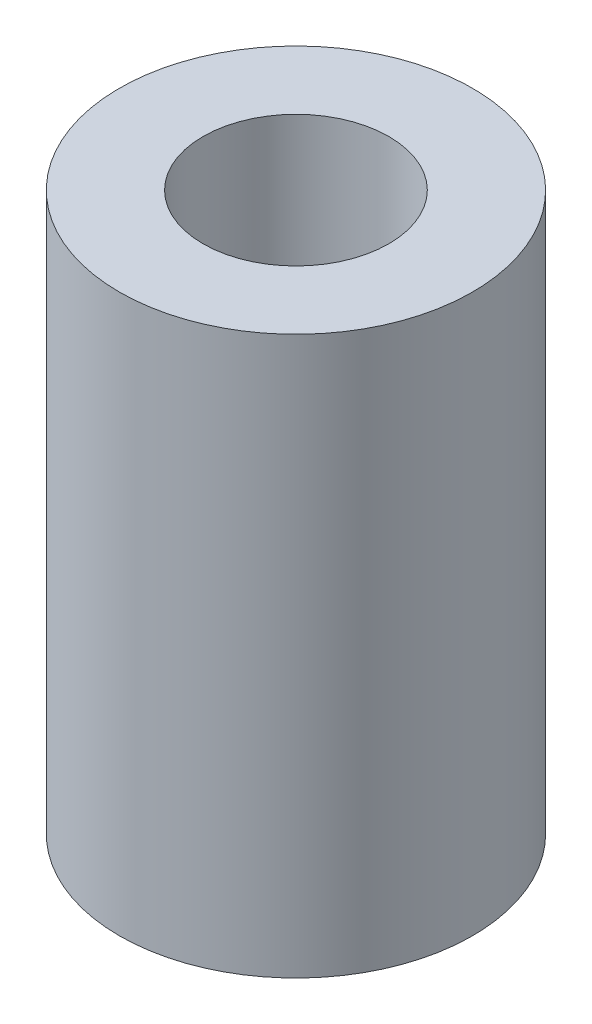
SolidWorks part; units mm, degrees
ref_plane "Front Plane" through (0, 0, 0) normal (0, 0, 1) x (1, 0, 0)
ref_plane "Top Plane" through (0, 0, 0) normal (0, 1, 0) x (1, 0, 0)
ref_plane "Right Plane" through (0, 0, 0) normal (1, 0, 0) x (0, 0, -1)
sketch "Sketch1" plane through (0, 0, 0) normal (0, 1, 0) x (1, 0, 0)
  circle A0 centre (0, 0) radius 9.5
  circle A1 centre (0, 0) radius 5
  dimension "D1" = 19
  dimension "D2" = 10
extrude "Boss-Extrude1" add sketch "Sketch1" along normal blind 30
